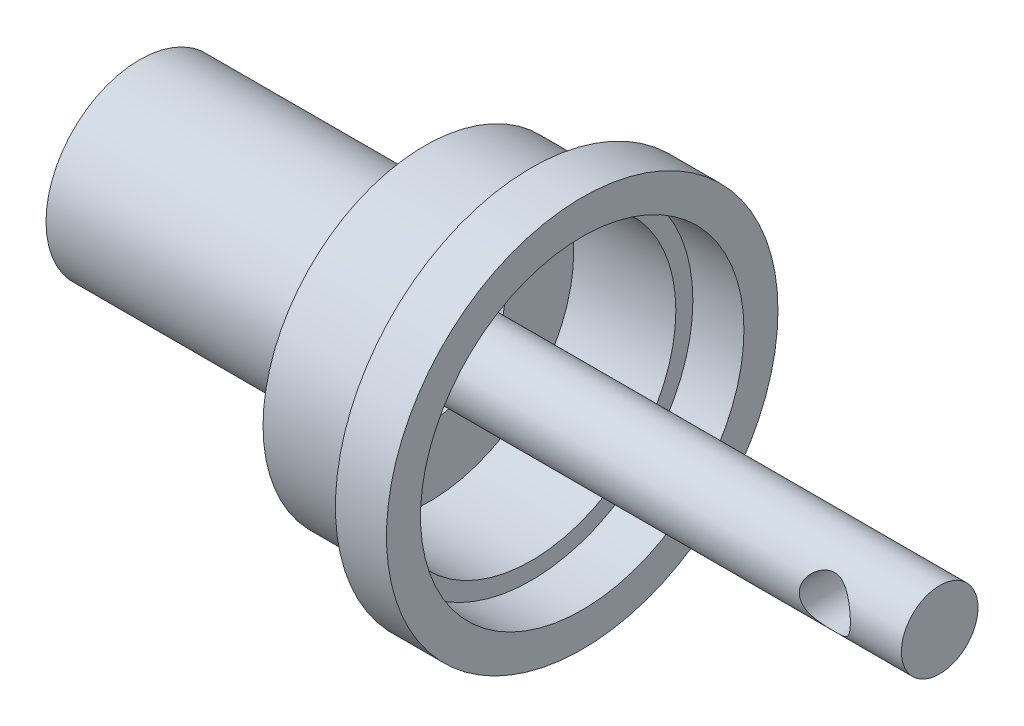
SolidWorks part; units mm, degrees
material "PVC 0.007 Plasticized"
ref_plane "Front Plane" through (0, 0, 0) normal (0, 0, 1) x (1, 0, 0)
ref_plane "Top Plane" through (0, 0, 0) normal (0, 1, 0) x (1, 0, 0)
ref_plane "Right Plane" through (0, 0, 0) normal (1, 0, 0) x (0, 0, -1)
sketch "Sketch1" plane through (0, 0, 0) normal (1, 0, 0) x (0, 0, -1)
  circle A0 centre (0, 0) radius 5.5
  dimension "D1" = 11
extrude "Boss-Extrude1" add sketch "Sketch1" along normal blind 5
sketch "Sketch2" plane through (5, 0, 0) normal (1, 0, 0) x (0, 0, -1)
  circle A0 centre (0, 0) radius 4.5
  circle A1 centre (0, 0) radius 5.5 construction
  circle A2 centre (0, 0) radius 5.5
  dimension "D1" = 9
extrude "Boss-Extrude2" add sketch "Sketch2" along normal blind 12
sketch "Sketch3" plane through (5, 0, 0) normal (1, 0, 0) x (0, 0, -1)
  circle A0 centre (0, 0) radius 2.25
  dimension "D1" = 4.5
extrude "Boss-Extrude3" add sketch "Sketch3" along normal blind 42
sketch "Sketch4" plane through (17, 0, 0) normal (1, 0, 0) x (0, 0, -1)
  circle A0 centre (0, 0) radius 9.5
  circle A1 centre (0, 0) radius 8.5
  dimension "D1" = 19
  dimension "D2" = 17
extrude "Boss-Extrude4" add sketch "Sketch4" along normal blind 6 separate body
sketch "Sketch5" plane through (17, 0, 0) normal (-1, 0, 0) x (0, 0, 1)
  circle A1 centre (0, 0) radius 9.5
  circle A2 centre (0, 0) radius 9.5
  dimension "D1" = 0
extrude "Boss-Extrude5" add sketch "Sketch5" along normal blind 0.25
sketch "Sketch6" plane through (23, 0, 0) normal (1, 0, 0) x (0, 0, -1)
  circle A0 centre (0, 0) radius 11.5
  circle A1 centre (0, 0) radius 9.5 construction
  circle A2 centre (0, 0) radius 9.5
  dimension "D1" = 23
extrude "Boss-Extrude6" add sketch "Sketch6" along normal blind 3 separate body
sketch "Sketch7" plane through (0, 0, 0) normal (0, 0, 1) x (1, 0, 0)
  line L0 (47, -2.25) -> (47, 2.25) construction
  line L1 (42.5, 0) -> (0, 0) construction
  circle A0 centre (42.5, 0) radius 1.5
  dimension "D1" = 3
  dimension "D2" = 4.5
extrude "Cut-Extrude1" cut sketch "Sketch7" against normal through all both and the other way through all
sketch "Sketch9" plane through (17, 0, 0) normal (1, 0, 0) x (0, 0, -1)
  circle A0 centre (0, 0) radius 4.5
  circle A1 centre (0, 0) radius 2.25 construction
  circle A2 centre (0, 0) radius 2.25
  dimension "D1" = 9
extrude "Cut-Extrude3" cut sketch "Sketch9" against normal blind 1 contours A0 | A2
